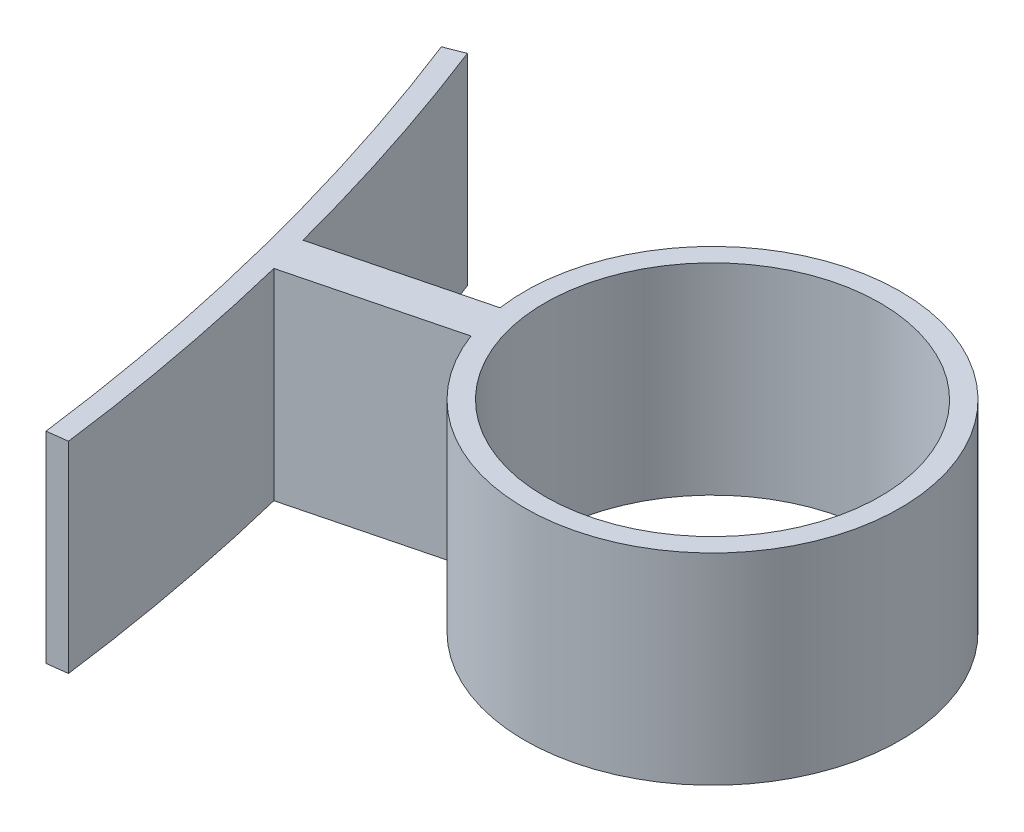
SolidWorks part; units mm, degrees
material "ASTM A36 Acero"
ref_plane "Alzado" through (0, 0, 0) normal (0, 0, 1) x (1, 0, 0)
ref_plane "Planta" through (0, 0, 0) normal (0, 1, 0) x (1, 0, 0)
ref_plane "Vista lateral" through (0, 0, 0) normal (1, 0, 0) x (0, 0, -1)
sketch "Croquis1" plane through (0, 0, 0) normal (0, 1, 0) x (1, 0, 0)
  line L1 (-53.297, -13.5803) -> (-24.2259, -6.1729)
  line L4 (-65.7974, 25.3652) -> (-63.0022, 26.4548)
  line L5 (-45.6362, -53.759) -> (-42.6604, -53.3781)
  line L7 (-51.1436, -9.9358) -> (-27.7176, -3.9667)
  line L10 (-49.6621, -15.75) -> (-26.2361, -9.7809)
  line L12 (-0.7519, 2.9043) -> (-0.7407, 2.9071)
  line L13 (0.7296, -2.91) -> (0.7407, -2.9071)
  circle A0 centre (0, 0) radius 25
  arc A1 (-26.2361, -9.7809) -> (-27.7176, -3.9667) centre (0, 0) ccw
  arc A3 (-45.6362, -53.759) -> (-65.7974, 25.3652) centre (-377.9245, -96.2969) ccw construction
  arc A4 (-65.7974, 25.3652) -> (-45.6362, -53.759) centre (-377.9245, -96.2969) cw
  arc A5 (-63.0022, 26.4548) -> (-51.1436, -9.9358) centre (-377.9245, -96.2969) cw
  arc A6 (-49.6621, -15.75) -> (-42.6604, -53.3781) centre (-377.9245, -96.2969) cw
  arc A7 (-63.0022, 26.4548) -> (-42.6604, -53.3781) centre (-377.9245, -96.2969) cw construction
  circle A8 centre (0, 0) radius 28 construction
  dimension "D1" = 50
  dimension "D2" = 3
  dimension "D5" = 3
extrude "Saliente-Extruir1" add sketch "Croquis1" along normal blind 30
